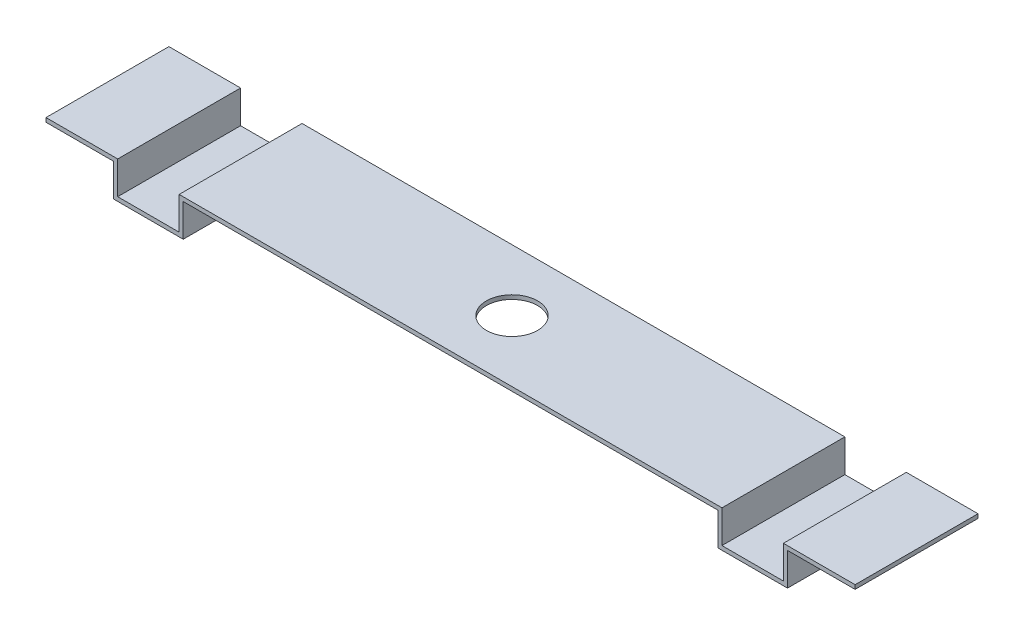
SolidWorks part; units mm, degrees
ref_plane "Front Plane" through (0, 0, 0) normal (0, 0, 1) x (1, 0, 0)
ref_plane "Top Plane" through (0, 0, 0) normal (0, 1, 0) x (1, 0, 0)
ref_plane "Right Plane" through (0, 0, 0) normal (1, 0, 0) x (0, 0, -1)
sketch "Sketch1" plane through (0, 0, 0) normal (0, 0, 1) x (1, 0, 0)
  line L0 (305.1429, 0) -> (272.1429, 0)
  line L1 (272.1429, 0) -> (272.1429, -15.9643)
  line L2 (272.1429, -15.9643) -> (238.1429, -15.9643)
  line L3 (238.1429, -15.9643) -> (238.1429, 0)
  line L4 (238.1429, 0) -> (-22.8571, 0)
  line L5 (-22.8571, 0) -> (-22.8571, -15.9643)
  line L6 (-22.8571, -15.9643) -> (-56.8571, -15.9643)
  line L7 (-56.8571, -15.9643) -> (-56.8571, 0)
  line L8 (-56.8571, 0) -> (-89.8571, 0)
  line L9 (-89.8571, 2) -> (-54.8571, 2)
  line L10 (-54.8571, 2) -> (-54.8571, -13.9643)
  line L11 (-54.8571, -13.9643) -> (-24.8571, -13.9643)
  line L12 (-24.8571, -13.9643) -> (-24.8571, 2)
  line L13 (-24.8571, 2) -> (240.1429, 2)
  line L14 (240.1429, 2) -> (240.1429, -13.9643)
  line L15 (240.1429, -13.9643) -> (270.1429, -13.9643)
  line L16 (270.1429, -13.9643) -> (270.1429, 2)
  line L17 (270.1429, 2) -> (305.1429, 2)
  line L18 (305.1429, 2) -> (305.1429, 0)
  line L19 (-89.8571, 2) -> (-89.8571, 0)
  point P20 (305.1429, 1)
  dimension "D1" = 35
  dimension "D2" = 35
  dimension "D3" = 30
  dimension "D4" = 30
  dimension "D5" = 395
  dimension "D6" = 34
  dimension "D7" = 2
  dimension "D8" = 2
  dimension "D9" = 2
  dimension "D10" = 2
  dimension "D11" = 2
  dimension "D12" = 2
  dimension "D13" = 2
  dimension "D14" = 34
  dimension "D15" = 15.9643
extrude "Boss-Extrude1" add sketch "Sketch1" against normal blind 60
sketch "Sketch2" plane through (0, 0, 0) normal (0, 1, 0) x (1, 0, 0)
  line L0 (-89.8571, 60) -> (-89.8571, 0) construction
  line L1 (240.1429, 0) -> (-24.8571, 0) construction
  circle A0 centre (107.6429, 30) radius 12.5
  point P4 (0, 0)
  point P6 (110.1748, 33.898)
  dimension "D1" = 25
  dimension "D2" = 197.5
  dimension "D3" = 30
extrude "Cut-Extrude2" cut sketch "Sketch2" along normal blind 60 contours A0
